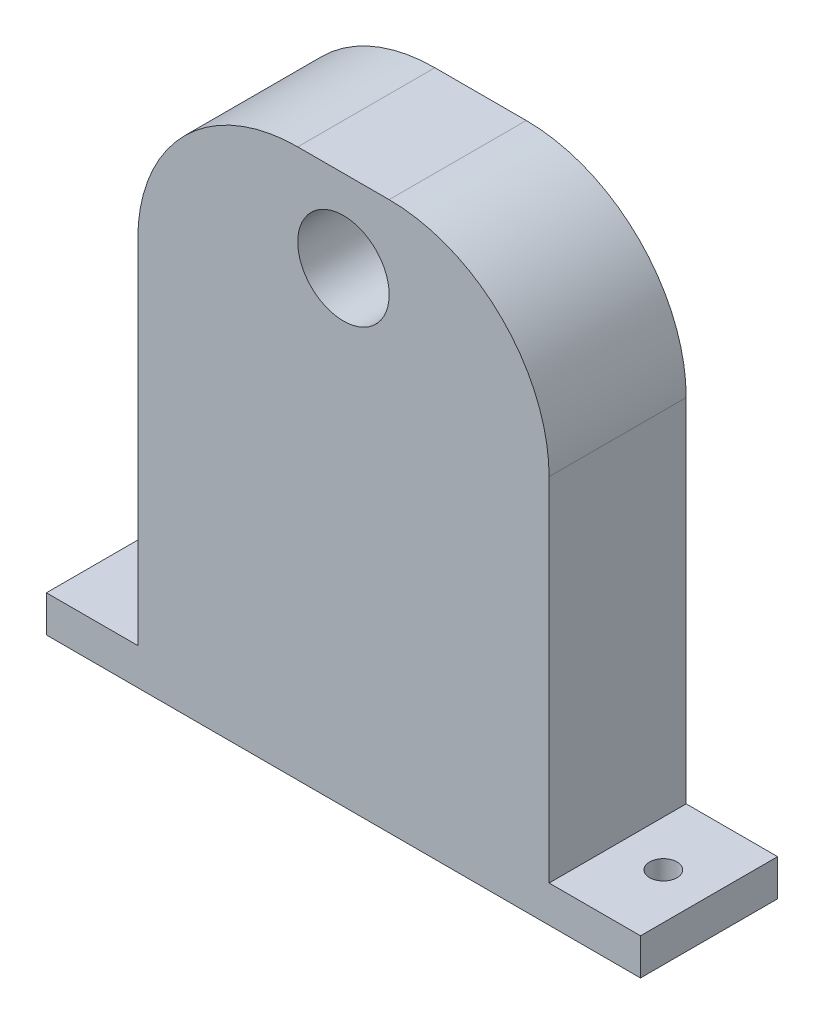
SolidWorks part; units mm, degrees
material "ABS"
ref_plane "Front Plane" through (0, 0, 0) normal (0, 0, 1) x (1, 0, 0)
ref_plane "Top Plane" through (0, 0, 0) normal (0, 1, 0) x (1, 0, 0)
ref_plane "Right Plane" through (0, 0, 0) normal (1, 0, 0) x (0, 0, -1)
sketch "Sketch1" plane through (0, 0, 0) normal (0, 1, 0) x (1, 0, 0)
  line L2 (-32.5, -7.5) -> (-32.5, 7.5)
  line L3 (-32.5, 7.5) -> (32.5, 7.5)
  line L4 (32.5, 7.5) -> (32.5, -7.5)
  line L5 (32.5, -7.5) -> (-32.5, -7.5)
extrude "Boss-Extrude1" add sketch "Sketch1" along normal blind 4
sketch "Sketch2" plane through (0, 4, 0) normal (0, 1, 0) x (1, 0, 0)
  line L1 (-32.5, -7.5) -> (32.5, -7.5) construction
  line L3 (-22.5, -7.5) -> (-22.5, 7.5)
  line L4 (32.5, 7.5) -> (-32.5, 7.5) construction
  line L5 (-22.5, 7.5) -> (22.5, 7.5)
  line L6 (22.5, 7.5) -> (22.5, -7.5)
  line L7 (22.5, -7.5) -> (-22.5, -7.5)
extrude "Boss-Extrude2" add sketch "Sketch2" along normal blind 56
sketch "Sketch3" plane through (0, 0, 7.5) normal (0, 0, 1) x (1, 0, 0)
  circle A0 centre (0, 51) radius 5
extrude "Cut-Extrude1" cut sketch "Sketch3" against normal blind 10
sketch "Sketch5" plane through (0, 4, 0) normal (0, 1, 0) x (1, 0, 0)
  circle A0 centre (-27.5, 0) radius 1.5
  circle A1 centre (27.5, 0) radius 1.5
extrude "Cut-Extrude4" cut sketch "Sketch5" against normal up to next
sketch "Sketch6" plane through (0, 0, 7.5) normal (0, 0, 1) x (1, 0, 0)
  line L1 (-22.5, 60) -> (22.5, 60) construction
  line L9 (22.5, 60) -> (22.5, 4) construction
  line L11 (5, 60) -> (22.5, 60)
  line L13 (22.5, 60) -> (22.5, 42.5)
  line L14 (-22.5, 42.5) -> (-22.5, 60)
  line L15 (-22.5, 60) -> (-5, 60)
  arc A4 (-5, 60) -> (-22.5, 42.5) centre (-5, 42.5) ccw
  arc A5 (22.5, 42.5) -> (5, 60) centre (5, 42.5) ccw
extrude "Cut-Extrude5" cut sketch "Sketch6" against normal up to next
